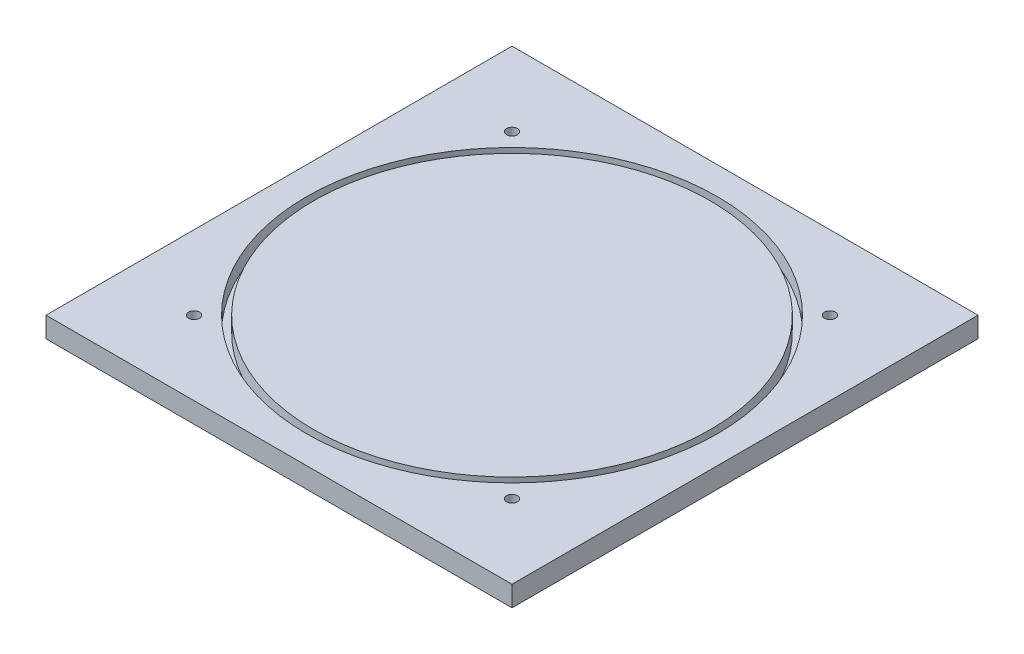
SolidWorks part; units mm, degrees
ref_plane "Front" through (0, 0, 0) normal (0, 0, 1) x (1, 0, 0)
ref_plane "Top" through (0, 0, 0) normal (0, 1, 0) x (1, 0, 0)
ref_plane "Right" through (0, 0, 0) normal (1, 0, 0) x (0, 0, -1)
sketch "Sketch1" plane through (0, 0, 0) normal (0, 1, 0) x (1, 0, 0)
  line L1 (144.78, -144.78) -> (-144.78, -144.78)
  line L2 (144.78, -144.78) -> (144.78, 144.78)
  line L3 (144.78, 144.78) -> (-144.78, 144.78)
  line L4 (-144.78, -144.78) -> (-144.78, 144.78)
  line L5 (144.78, -144.78) -> (-144.78, 144.78) construction
  line L6 (144.78, 144.78) -> (-144.78, -144.78) construction
  circle A0 centre (0, 0) radius 144.78 construction
  dimension "D1" = 289.56
  dimension "D2" = 289.56
extrude "Boss-Extrude1" add sketch "Sketch1" along normal blind 12.7
sketch "Sketch7" plane through (0, 12.7, 0) normal (0, 1, 0) x (1, 0, 0)
  circle A0 centre (0, 0) radius 127.635
  circle A1 centre (0, 0) radius 123.19
  dimension "D1" = 246.38
  dimension "D2" = 255.27
extrude "Cut-Extrude1" cut sketch "Sketch7" against normal blind 9.525
hole_wizard "1/4 Clearance Hole1" positions "Sketch6" profile "Sketch5" hole size "1/4" standard "ANSI Inch" end condition through all
sketch "Sketch6" plane through (0, 0, 0) normal (0, -1, 0) x (-1, 0, 0)
  line L0 (0, 0) -> (0, -196.9955) construction
  line L2 (0, 0) -> (98.7828, -98.7828) construction
  point P0 (98.7828, -98.7828)
  dimension "D1" = 139.7
  dimension "D2" = 45
sketch "Sketch5" plane through (-98.7828, 0, 98.7828) normal (1, 0, 0) x (0, 0, -1)
  line L0 (0, 0) -> (0, 12.7)
  line L1 (0, 12.7) -> (3.3782, 12.7)
  line L2 (3.3782, 12.7) -> (3.3782, 0)
  line L5 (3.3782, 0) -> (0, 0)
  line L11 (0, -6.35) -> (0, 107.95) construction
  dimension "Thru Hole Dia." = 6.7564
  dimension "Thru Hole Depth" = 12.7
pattern_circular "CirPattern1" count 4 over 360 about axis through (0, 0, 0) along (0, 1, 0) of "1/4 Clearance Hole1"
